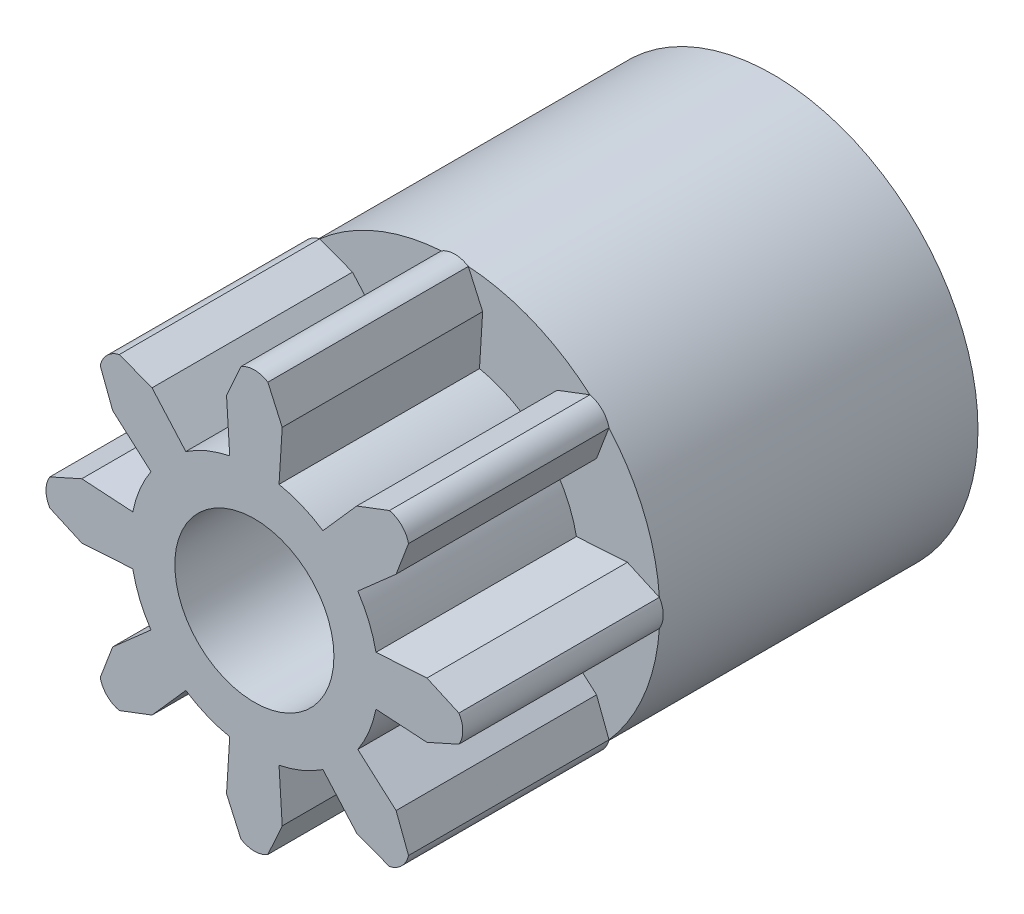
SolidWorks part; units mm, degrees
ref_plane "Przednia" through (0, 0, 0) normal (0, 0, 1) x (1, 0, 0)
ref_plane "Górna" through (0, 0, 0) normal (0, 1, 0) x (1, 0, 0)
ref_plane "Prawa" through (0, 0, 0) normal (1, 0, 0) x (0, 0, -1)
sketch "Szkic1" plane through (0, 0, 0) normal (0, 0, 1) x (1, 0, 0)
  line L0 (0, 0) -> (0, 7.2138) construction
  line L1 (0.875, 5.4234) -> (0.775, 3.8222)
  line L2 (0.875, 5.4234) -> (0.4241, 6.4277)
  line L3 (-0.875, 5.4234) -> (-0.4241, 6.4277)
  line L4 (-0.875, 5.4234) -> (-0.775, 3.8222)
  line L5 (4.4536, 3.2162) -> (3.2507, 2.1547)
  line L6 (4.4536, 3.2162) -> (4.845, 4.2452)
  line L7 (3.2162, 4.4536) -> (4.2452, 4.845)
  line L8 (3.2162, 4.4536) -> (2.1547, 3.2507)
  line L9 (0, 0) -> (5.1009, 5.1009) construction
  line L10 (5.4234, -0.875) -> (3.8222, -0.775)
  line L11 (5.4234, -0.875) -> (6.4277, -0.4241)
  line L12 (5.4234, 0.875) -> (6.4277, 0.4241)
  line L13 (5.4234, 0.875) -> (3.8222, 0.775)
  line L14 (0, 0) -> (7.2138, 0) construction
  line L15 (3.2162, -4.4536) -> (2.1547, -3.2507)
  line L16 (3.2162, -4.4536) -> (4.2452, -4.845)
  line L17 (4.4536, -3.2162) -> (4.845, -4.2452)
  line L18 (4.4536, -3.2162) -> (3.2507, -2.1547)
  line L19 (0, 0) -> (5.1009, -5.1009) construction
  line L20 (-0.875, -5.4234) -> (-0.775, -3.8222)
  line L21 (-0.875, -5.4234) -> (-0.4241, -6.4277)
  line L22 (0.875, -5.4234) -> (0.4241, -6.4277)
  line L23 (0.875, -5.4234) -> (0.775, -3.8222)
  line L24 (0, 0) -> (0, -7.2138) construction
  line L25 (-4.4536, -3.2162) -> (-3.2507, -2.1547)
  line L26 (-4.4536, -3.2162) -> (-4.845, -4.2452)
  line L27 (-3.2162, -4.4536) -> (-4.2452, -4.845)
  line L28 (-3.2162, -4.4536) -> (-2.1547, -3.2507)
  line L29 (0, 0) -> (-5.1009, -5.1009) construction
  line L30 (-5.4234, 0.875) -> (-3.8222, 0.775)
  line L31 (-5.4234, 0.875) -> (-6.4277, 0.4241)
  line L32 (-5.4234, -0.875) -> (-6.4277, -0.4241)
  line L33 (-5.4234, -0.875) -> (-3.8222, -0.775)
  line L34 (0, 0) -> (-7.2138, 0) construction
  line L35 (-3.2162, 4.4536) -> (-2.1547, 3.2507)
  line L36 (-3.2162, 4.4536) -> (-4.2452, 4.845)
  line L37 (-4.4536, 3.2162) -> (-4.845, 4.2452)
  line L38 (-4.4536, 3.2162) -> (-3.2507, 2.1547)
  line L39 (0, 0) -> (-5.1009, 5.1009) construction
  circle A0 centre (0, 0) radius 2.5
  circle A1 centre (0, 0) radius 6.55 construction
  arc A2 (-0.775, 3.8222) -> (0.775, 3.8222) centre (0, 0) ccw construction
  arc A3 (0.4241, 6.4277) -> (0, 6.55) centre (0, 5.7533) ccw
  arc A4 (-0.4241, 6.4277) -> (0, 6.55) centre (0, 5.7533) cw
  circle A5 centre (0, 0) radius 2.5
  arc A6 (4.845, 4.2452) -> (4.6315, 4.6315) centre (4.0682, 4.0682) ccw
  arc A7 (4.2452, 4.845) -> (4.6315, 4.6315) centre (4.0682, 4.0682) cw
  circle A8 centre (0, 0) radius 6.55 construction
  circle A9 centre (0, 0) radius 3.9 construction
  circle A10 centre (0, 0) radius 2.5
  arc A11 (6.4277, -0.4241) -> (6.55, 0) centre (5.7533, 0) ccw
  arc A12 (6.4277, 0.4241) -> (6.55, 0) centre (5.7533, 0) cw
  circle A13 centre (0, 0) radius 6.55 construction
  circle A14 centre (0, 0) radius 3.9 construction
  circle A15 centre (0, 0) radius 2.5
  arc A16 (4.2452, -4.845) -> (4.6315, -4.6315) centre (4.0682, -4.0682) ccw
  arc A17 (4.845, -4.2452) -> (4.6315, -4.6315) centre (4.0682, -4.0682) cw
  circle A18 centre (0, 0) radius 6.55 construction
  circle A19 centre (0, 0) radius 3.9 construction
  circle A20 centre (0, 0) radius 2.5
  arc A21 (-0.4241, -6.4277) -> (0, -6.55) centre (0, -5.7533) ccw
  arc A22 (0.4241, -6.4277) -> (0, -6.55) centre (0, -5.7533) cw
  circle A23 centre (0, 0) radius 6.55 construction
  circle A24 centre (0, 0) radius 3.9 construction
  circle A25 centre (0, 0) radius 2.5
  arc A26 (-4.845, -4.2452) -> (-4.6315, -4.6315) centre (-4.0682, -4.0682) ccw
  arc A27 (-4.2452, -4.845) -> (-4.6315, -4.6315) centre (-4.0682, -4.0682) cw
  circle A28 centre (0, 0) radius 6.55 construction
  circle A29 centre (0, 0) radius 3.9 construction
  circle A30 centre (0, 0) radius 2.5
  arc A31 (-6.4277, 0.4241) -> (-6.55, 0) centre (-5.7533, 0) ccw
  arc A32 (-6.4277, -0.4241) -> (-6.55, 0) centre (-5.7533, 0) cw
  circle A33 centre (0, 0) radius 6.55 construction
  circle A34 centre (0, 0) radius 3.9 construction
  circle A35 centre (0, 0) radius 2.5
  arc A36 (-4.2452, 4.845) -> (-4.6315, 4.6315) centre (-4.0682, 4.0682) ccw
  arc A37 (-4.845, 4.2452) -> (-4.6315, 4.6315) centre (-4.0682, 4.0682) cw
  circle A38 centre (0, 0) radius 6.55 construction
  circle A39 centre (0, 0) radius 3.9 construction
  arc A40 (-0.775, 3.8222) -> (-2.1547, 3.2507) centre (0, 0) ccw
  arc A41 (-3.2507, 2.1547) -> (-3.8222, 0.775) centre (0, 0) ccw
  arc A42 (-3.8222, -0.775) -> (-3.2507, -2.1547) centre (0, 0) ccw
  arc A43 (-2.1547, -3.2507) -> (-0.775, -3.8222) centre (0, 0) ccw
  arc A44 (0.775, -3.8222) -> (2.1547, -3.2507) centre (0, 0) ccw
  arc A45 (3.2507, -2.1547) -> (3.8222, -0.775) centre (0, 0) ccw
  arc A46 (3.8222, 0.775) -> (3.2507, 2.1547) centre (0, 0) ccw
  arc A47 (2.1547, 3.2507) -> (0.775, 3.8222) centre (0, 0) ccw
  point P108 (0, 0)
  dimension "D1" = 5
  dimension "D2" = 13.1
  dimension "D3" = 7.8
  dimension "D4" = 1.75
  dimension "D5" = 1.55
extrude "Dodanie-wyciągnięcie1" add sketch "Szkic1" along normal blind 6.3 contours L8 A47 L1 L2 A3 A4 L3 L4 A40 L35 L36 A36 A37 L37 L38 A41 L30 L31 A31 A32 L32 L33 A42 L25 L26 A26 A27 L27 L28 A43 L20 L21 A21 A22 L22 L23 A44 L15 L16 A16 A17 L17 L18 A45 L10 L11 A11 A12 L12 L13 A46
sketch "Sketch1" plane through (0, 0, 0) normal (0, 0, 1) x (1, 0, 0)
  circle A0 centre (0, 0) radius 6.4417
  circle A1 centre (0, 0) radius 2.5
extrude "Boss-Extrude1" add sketch "Sketch1" against normal blind 10
